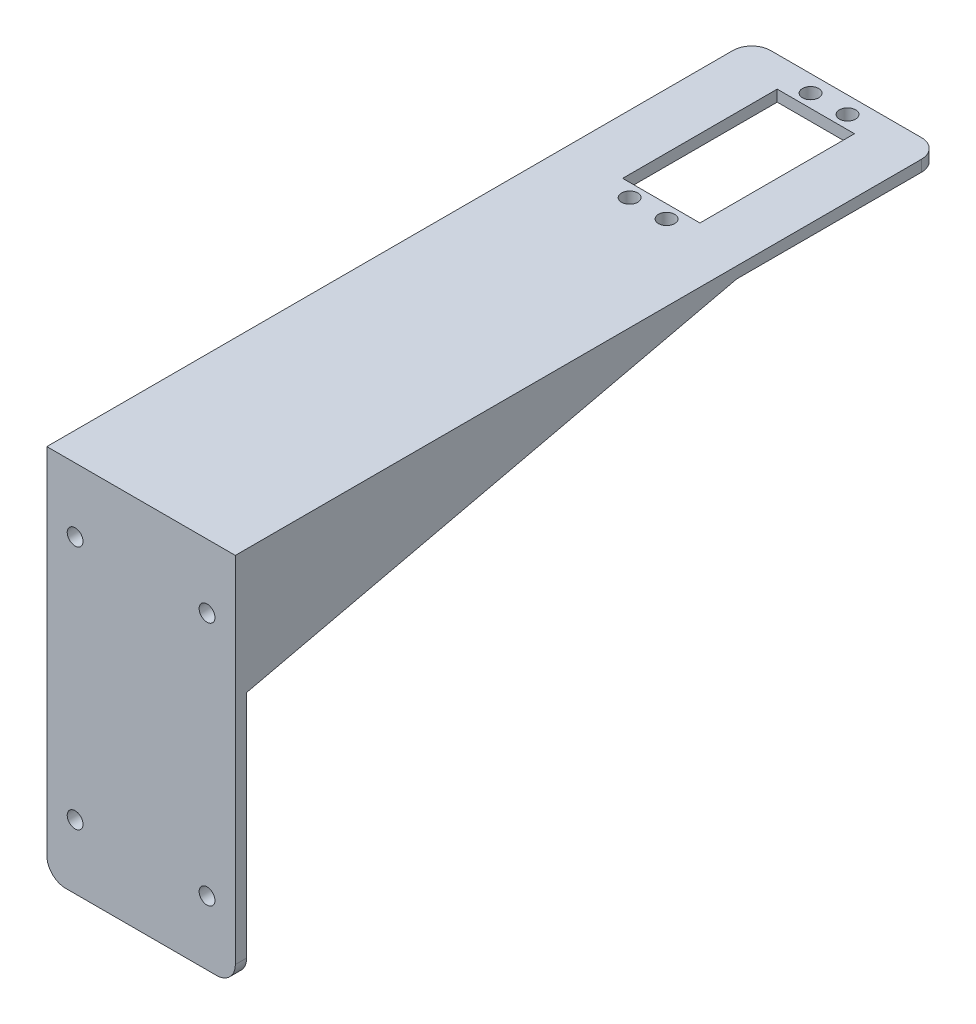
SolidWorks part; units mm, degrees
ref_plane "前视基准面" through (0, 0, 0) normal (0, 0, 1) x (1, 0, 0)
ref_plane "上视基准面" through (0, 0, 0) normal (0, 1, 0) x (1, 0, 0)
ref_plane "右视基准面" through (0, 0, 0) normal (1, 0, 0) x (0, 0, -1)
sketch "草图1" plane through (0, 0, 0) normal (0, 1, 0) x (1, 0, 0)
  line L1 (-25, 93.5) -> (25, 93.5)
  line L2 (-25, 93.5) -> (-25, -93.5)
  line L3 (-25, -93.5) -> (25, -93.5)
  line L4 (25, 93.5) -> (25, -93.5)
  line L5 (-25, 93.5) -> (25, -93.5) construction
  line L6 (-25, -93.5) -> (25, 93.5) construction
  point P0 (0, 0)
  dimension "D1" = 50
  dimension "D2" = 187
extrude "凸台-拉伸1" add sketch "草图1" along normal blind 3
sketch "草图4" plane through (0, 0, 0) normal (0, -1, 0) x (1, 0, 0)
  line L0 (0, 0) -> (0, -133.72) construction
  line L1 (25, -93.5) -> (-25, -93.5) construction
  line L2 (-10.25, -44.5) -> (10.25, -44.5)
  line L3 (-10.25, -44.5) -> (-10.25, -85.5)
  line L4 (-10.25, -85.5) -> (10.25, -85.5)
  line L5 (10.25, -44.5) -> (10.25, -85.5)
  line L6 (-10.25, -44.5) -> (10.25, -85.5) construction
  line L7 (-10.25, -85.5) -> (10.25, -44.5) construction
  line L8 (0, -65) -> (-40.0728, -65) construction
  circle A0 centre (-4.9, -89) radius 2.15
  circle A1 centre (4.9, -89) radius 2.15
  circle A2 centre (4.9, -41) radius 2.15
  circle A3 centre (-4.9, -41) radius 2.15
  point P3 (0, -65)
  dimension "D4" = 4.3
  dimension "D1" = 20.5
  dimension "D2" = 41
  dimension "D3" = 8
  dimension "D5" = 48
  dimension "D6" = 9.8
extrude "切除-拉伸2" cut sketch "草图4" against normal through all
sketch "草图5" plane through (0, 0, 0) normal (0, -1, 0) x (1, 0, 0)
  line L0 (25, 93.5) -> (25, -93.5) construction
  line L1 (-25, 93.5) -> (25, 93.5)
  line L2 (-25, 93.5) -> (-25, 90.5)
  line L3 (-25, 90.5) -> (25, 90.5)
  line L4 (25, 93.5) -> (25, 90.5)
  dimension "D1" = 3
extrude "凸台-拉伸2" add sketch "草图5" along normal blind 96
sketch "草图6" plane through (0, 0, 93.5) normal (0, 0, 1) x (1, 0, 0)
  line L0 (-25, 3) -> (25, -96) construction
  line L1 (-25, -96) -> (25, 3) construction
  line L2 (0, -46.5) -> (0, 17.8163) construction
  line L3 (0, -46.5) -> (-76.6044, -46.5) construction
  circle A0 centre (-17.5, -14) radius 2.1
  circle A1 centre (17.5, -14) radius 2.1
  circle A2 centre (17.5, -79) radius 2.1
  circle A3 centre (-17.5, -79) radius 2.1
  dimension "D1" = 4.2
  dimension "D2" = 35
  dimension "D3" = 65
extrude "切除-拉伸3" cut sketch "草图6" against normal through all
fillet "圆角1" radius 5 4 edges at (-25, -96, 92) (25, -96, 92) (25, 1.5, -93.5) (-25, 1.5, -93.5)
sketch "草图7" plane through (25, 0, 0) normal (1, 0, 0) x (0, 0, -1)
  line L0 (39.5, 0) -> (-90.5, -30)
  line L1 (-90.5, 0) -> (88.5, 0) construction
  line L2 (-90.5, -91) -> (-90.5, 0) construction
  line L3 (-90.5, -30) -> (-90.5, 0)
  line L4 (-90.5, 0) -> (39.5, 0)
  dimension "D1" = 130
  dimension "D2" = 30
extrude "凸台-拉伸3" add sketch "草图7" against normal blind 2
sketch "草图9" plane through (-25, 0, 0) normal (-1, 0, 0) x (0, 0, 1)
  line L3 (-39.5, 0) -> (90.5, -30)
  line L4 (90.5, -30) -> (90.5, 0)
  line L5 (90.5, 0) -> (-39.5, 0)
  line L6 (-39.5, 0) -> (90.5, -30)
  line L7 (90.5, -30) -> (90.5, 0)
  line L8 (90.5, 0) -> (-39.5, 0)
  dimension "D1" = 0
extrude "凸台-拉伸4" add sketch "草图9" against normal blind 2
